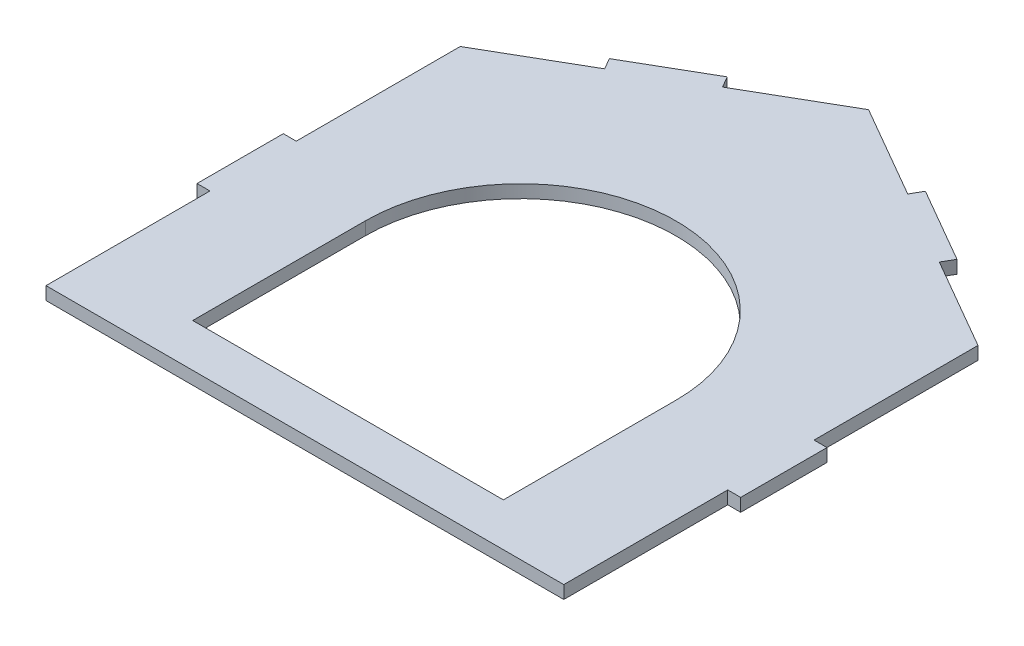
SolidWorks part; units mm, degrees
ref_plane "Alzado" through (0, 0, 0) normal (0, 0, 1) x (1, 0, 0)
ref_plane "Planta" through (0, 0, 0) normal (0, 1, 0) x (1, 0, 0)
ref_plane "Vista lateral" through (0, 0, 0) normal (1, 0, 0) x (0, 0, -1)
sketch "Sketch1" plane through (0, 0, 0) normal (0, 1, 0) x (1, 0, 0)
  line L0 (0, 705.3972) -> (0, 0) construction
  line L1 (-300, -240) -> (300, -240)
  line L2 (-300, -240) -> (-300, -50)
  line L3 (-300, 240) -> (300, 240) construction
  line L5 (-300, -240) -> (300, 240) construction
  line L6 (-300, 240) -> (300, -240) construction
  line L7 (-300, 240) -> (-193.9119, 301.25)
  line L8 (0, 413.2051) -> (107.3093, 351.25)
  line L9 (-300, -50) -> (-300, 50) construction
  line L10 (300, 240) -> (300, 50)
  line L19 (-300, 50) -> (-300, 240)
  line L20 (-300, 50) -> (-315, 50)
  line L21 (-315, 50) -> (-315, -50)
  line L22 (-315, -50) -> (-300, -50)
  line L23 (315, -50) -> (300, -50)
  line L24 (315, 50) -> (315, -50)
  line L25 (300, 50) -> (315, 50)
  line L26 (300, -50) -> (300, -240)
  line L28 (-193.9119, 301.25) -> (-201.4119, 314.2404)
  line L29 (-201.4119, 314.2404) -> (-114.8093, 364.2404)
  line L30 (-114.8093, 364.2404) -> (-107.3093, 351.25)
  line L31 (-107.3093, 351.25) -> (0, 413.2051)
  line L32 (114.8093, 364.2404) -> (107.3093, 351.25)
  line L33 (201.4119, 314.2404) -> (114.8093, 364.2404)
  line L34 (193.9119, 301.25) -> (201.4119, 314.2404)
  line L35 (193.9119, 301.25) -> (300, 240)
  point P0 (0, 0)
  point P12 (-300, 0)
  point P14 (-300, 0)
  point P22 (-125, 272.1688)
extrude "Boss-Extrude1" add sketch "Sketch1" along normal blind 15
sketch "Sketch2" plane through (0, 15, 0) normal (0, 1, 0) x (1, 0, 0)
  line L0 (0, 262.7005) -> (0, -339.4962) construction
  line L5 (-180, -190) -> (180, -190)
  line L6 (180, -190) -> (180, 10)
  line L7 (-180, -190) -> (-180, 10)
  line L8 (-300, -240) -> (300, -240) construction
  arc A0 (-180, 10) -> (180, 10) centre (0, 10) cw
  point P5 (0, -190)
  dimension "D1" = 50
  dimension "D2" = 180
  dimension "D3" = 200
  dimension "D4" = 360
extrude "Cut-Extrude2" cut sketch "Sketch2" against normal up to next
equation "\"Scale\"= 1.2"
equation "\"Width\" = 40 * \"Scale\""
equation "\"Long\"= 50 * \"Scale\""
equation "\"D1@Sketch1\"=\"Width\""
equation "\"D2@Sketch1\"=\"Long\""
